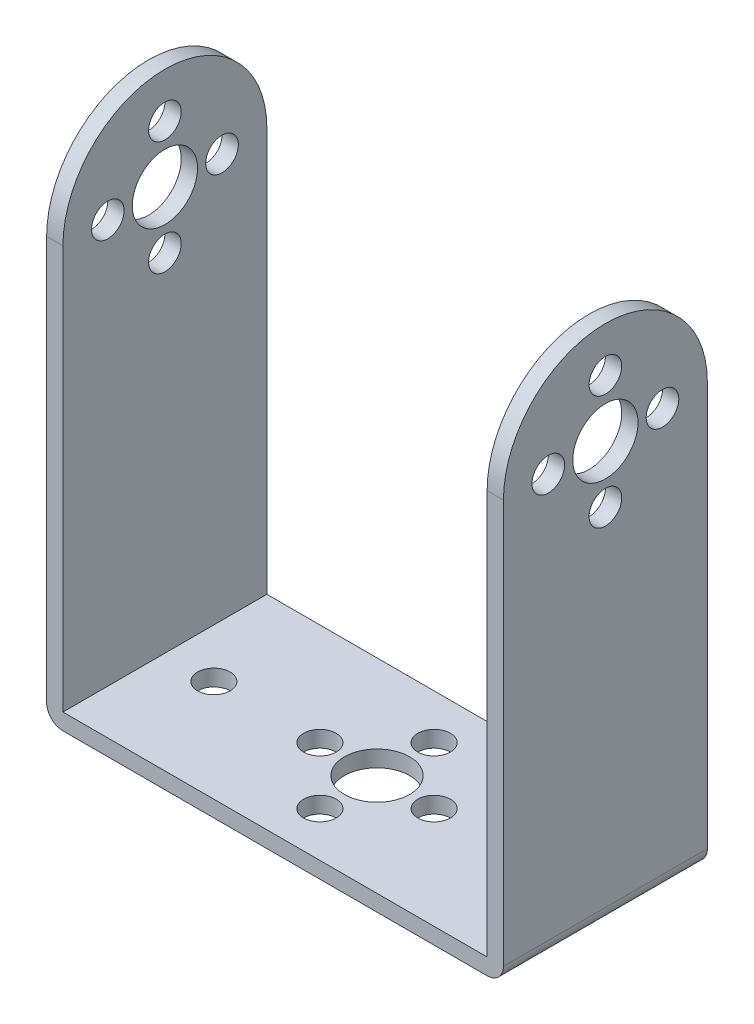
SolidWorks part; units mm, degrees
material "可锻铸铁"
ref_plane "前视基准面" through (0, 0, 0) normal (0, 0, 1) x (1, 0, 0)
ref_plane "上视基准面" through (0, 0, 0) normal (0, 1, 0) x (1, 0, 0)
ref_plane "右视基准面" through (0, 0, 0) normal (1, 0, 0) x (0, 0, -1)
sketch "草图2" plane through (0, 0, 0) normal (1, 0, 0) x (0, 0, -1)
  line L2 (-23.2496, 25.75) -> (-23.2496, -25.75)
  line L3 (-23.2496, -25.75) -> (1.7504, -25.75)
  line L4 (1.7504, 25.75) -> (1.7504, -25.75)
  arc A1 (1.7504, 25.75) -> (-23.2496, 25.75) centre (-10.7496, 25.75) ccw
  circle A2 centre (-10.7496, 25.75) radius 4
  circle A3 centre (-10.7496, 32.75) radius 2
  circle A4 centre (-17.7496, 25.75) radius 2
  circle A5 centre (-10.7496, 18.75) radius 2
  circle A6 centre (-3.7496, 25.75) radius 2
  point P0 (0, 0)
  dimension "D3" = 12.5
  dimension "D4" = 8
  dimension "D5" = 4
  dimension "D1" = 25
  dimension "D2" = 51.5
  dimension "D6" = 7
  dimension "D7" = 4
extrude "凸台-拉伸1" add sketch "草图2" along normal blind 56
sketch "草图3" plane through (0, 0, -1.7504) normal (0, 0, -1) x (-1, 0, 0)
  line L0 (0, -25.75) -> (0, 25.75) construction
  line L1 (-54, 40.25) -> (-2, 40.25)
  line L2 (-54, 40.25) -> (-54, -23.75)
  line L3 (-54, -23.75) -> (-2, -23.75)
  line L4 (-2, 40.25) -> (-2, -23.75)
  line L5 (-54, 40.25) -> (-2, -23.75) construction
  line L6 (-54, -23.75) -> (-2, 40.25) construction
  line L7 (-56, -25.75) -> (-56, 25.75) construction
  line L8 (-56, -25.75) -> (0, -25.75) construction
  point P0 (-28, 8.25)
  dimension "D1" = 2
  dimension "D2" = 2
  dimension "D3" = 2
  dimension "D4" = 64
extrude "切除-拉伸1" cut sketch "草图3" against normal up to next
sketch "草图4" plane through (0, -23.75, 0) normal (0, 1, 0) x (1, 0, 0)
  line L0 (54, -23.2496) -> (54, 1.7504) construction
  line L2 (2, -23.2496) -> (54, -23.2496) construction
  circle A0 centre (28, -10.7496) radius 4
  circle A1 centre (35, -10.7496) radius 2
  circle A2 centre (28, -17.7496) radius 2
  circle A3 centre (21, -10.7496) radius 2
  circle A4 centre (28, -3.7496) radius 2
  circle A5 centre (8, -10.7496) radius 2
  circle A6 centre (48, -10.7496) radius 2
  dimension "D1" = 8
  dimension "D2" = 4
  dimension "D8" = 4
  dimension "D11" = 4
  dimension "D3" = 7
  dimension "D4" = 26
  dimension "D5" = 12.5
  dimension "D6" = 12.5
  dimension "D9" = 20
  dimension "D10" = 12.5
  dimension "D12" = 20
  dimension "D13" = 12.5
  dimension "D7" = 4
extrude "切除-拉伸2" cut sketch "草图4" against normal up to next
fillet "圆角1" radius 2 1 edges at (56, -25.75, 10.7496)
fillet "圆角2" radius 2 1 edges at (0, -25.75, 10.7496)
